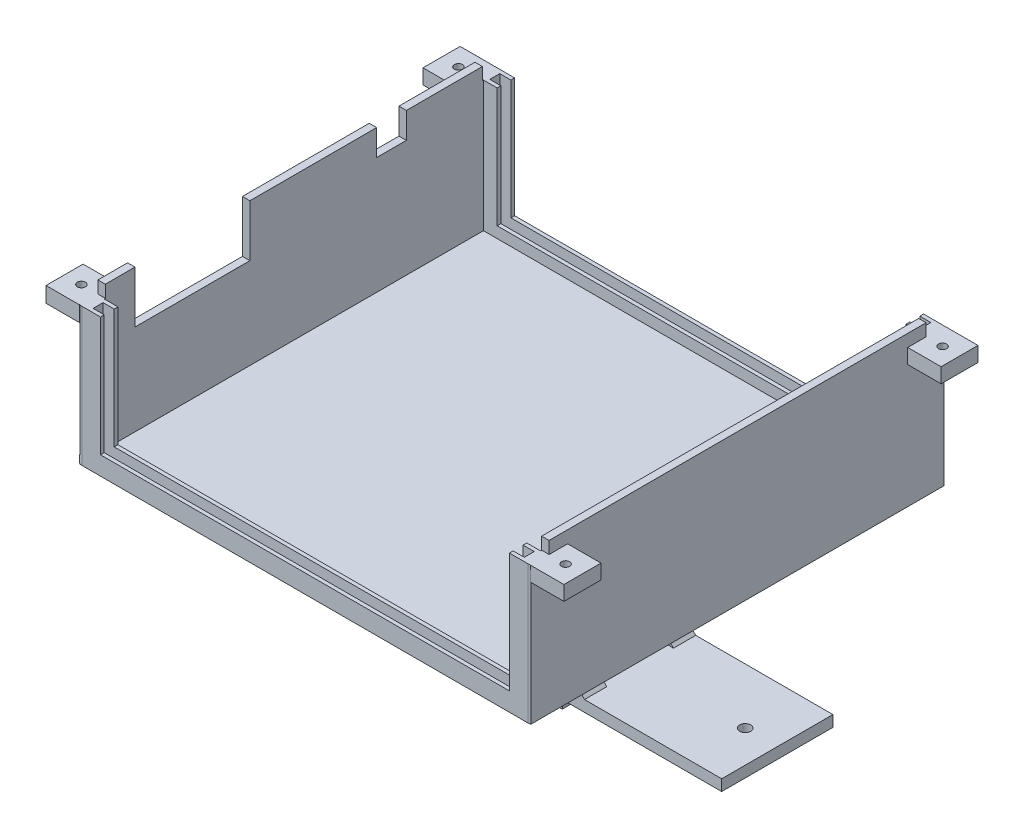
SolidWorks part; units mm, degrees
ref_plane "Front Plane" through (0, 0, 0) normal (0, 0, 1) x (1, 0, 0)
ref_plane "Top Plane" through (0, 0, 0) normal (0, 1, 0) x (1, 0, 0)
ref_plane "Right Plane" through (0, 0, 0) normal (1, 0, 0) x (0, 0, -1)
sketch "Sketch1" plane through (0, 0, 0) normal (0, 1, 0) x (1, 0, 0)
  line L1 (0, 0) -> (124.4, 0)
  line L2 (0, 0) -> (0, 111.7)
  line L3 (0, 111.7) -> (124.4, 111.7)
  line L4 (124.4, 0) -> (124.4, 111.7)
  dimension "D1" = 124.4
  dimension "D2" = 111.7
extrude "Boss-Extrude1" add sketch "Sketch1" along normal blind 2
sketch "Sketch2" plane through (0, 2, 0) normal (0, 1, 0) x (1, 0, 0)
  line L1 (124.4, 111.7) -> (0, 111.7) construction
  line L2 (123.05, 5) -> (121.05, 5)
  line L3 (123.05, 5) -> (123.05, 106.7)
  line L4 (123.05, 106.7) -> (121.05, 106.7)
  line L5 (121.05, 5) -> (121.05, 106.7)
  line L6 (124.4, 0) -> (124.4, 111.7) construction
  line L7 (0, 0) -> (124.4, 0) construction
  line L8 (0, 111.7) -> (0, 0) construction
  line L9 (3.35, 5) -> (1.35, 5)
  line L10 (3.35, 5) -> (3.35, 106.7)
  line L11 (3.35, 106.7) -> (1.35, 106.7)
  line L12 (1.35, 5) -> (1.35, 106.7)
  dimension "D1" = 2
  dimension "D2" = 5
  dimension "D3" = 1.35
  dimension "D4" = 5
  dimension "D5" = 1.35
  dimension "D6" = 2
  dimension "D7" = 5
  dimension "D8" = 5
extrude "Boss-Extrude2" add sketch "Sketch2" along normal blind 38.5
sketch "Sketch3" plane through (0, 2, 0) normal (0, 1, 0) x (1, 0, 0)
  line L1 (123.05, 0) -> (1.35, 0)
  line L2 (123.05, 0) -> (123.05, 4.7)
  line L3 (123.05, 4.7) -> (1.35, 4.7)
  line L4 (1.35, 0) -> (1.35, 4.7)
  line L5 (124.4, 0) -> (124.4, 111.7) construction
  dimension "D1" = 4.7
  dimension "D2" = 1.35
  dimension "D3" = 1.35
extrude "Boss-Extrude3" add sketch "Sketch3" along normal blind 3
sketch "Sketch5" plane through (0, 5, 0) normal (0, 1, 0) x (1, 0, 0)
  line L1 (120.35, 3.7) -> (4.05, 3.7)
  line L2 (120.35, 3.7) -> (120.35, 1)
  line L3 (120.35, 1) -> (4.05, 1)
  line L4 (4.05, 3.7) -> (4.05, 1)
  line L6 (1.35, 4.7) -> (1.35, 0) construction
  line L10 (123.05, 0) -> (123.05, 4.7) construction
  line L11 (123.05, 0) -> (123.05, 4.7) construction
  line L12 (1.35, 4.7) -> (1.35, 0) construction
  line L13 (123.05, 4.7) -> (1.35, 4.7) construction
  dimension "D2" = 2.7
  dimension "D3" = 2.7
  dimension "D4" = 2.7
  dimension "D5" = 2.7
  dimension "D6" = 2.7
  dimension "D7" = 1
  dimension "D8" = 1
extrude "Cut-Extrude8" cut sketch "Sketch5" against normal blind 3
sketch "Sketch14" plane through (0, 2, 0) normal (0, 1, 0) x (1, 0, 0)
  line L1 (1.35, 111.7) -> (123.05, 111.7)
  line L2 (1.35, 111.7) -> (1.35, 107)
  line L3 (1.35, 107) -> (123.05, 107)
  line L4 (123.05, 111.7) -> (123.05, 107)
  dimension "D1" = 4.7
  dimension "D2" = 1.35
  dimension "D3" = 1.35
extrude "Boss-Extrude6" add sketch "Sketch14" along normal blind 3
sketch "Sketch15" plane through (0, 5, 0) normal (0, 1, 0) x (1, 0, 0)
  line L1 (4.05, 110.7) -> (120.35, 110.7)
  line L2 (4.05, 110.7) -> (4.05, 108)
  line L3 (4.05, 108) -> (120.35, 108)
  line L4 (120.35, 110.7) -> (120.35, 108)
  line L8 (123.05, 107) -> (123.05, 111.7) construction
  line L9 (1.35, 106.7) -> (1.35, 5) construction
  line L10 (123.05, 111.7) -> (1.35, 111.7) construction
  dimension "D1" = 2.7
  dimension "D2" = 2.7
  dimension "D3" = 2.7
  dimension "D4" = 1
extrude "Cut-Extrude14" cut sketch "Sketch15" against normal blind 3
sketch "Sketch18" plane through (0, 2, 0) normal (0, 1, 0) x (1, 0, 0)
  line L2 (3.35, 106.7) -> (1.35, 106.7)
  line L3 (3.35, 106.7) -> (3.35, 107)
  line L4 (3.35, 107) -> (1.35, 107)
  line L5 (1.35, 106.7) -> (1.35, 107)
  line L6 (121.05, 106.7) -> (123.05, 106.7)
  line L7 (121.05, 106.7) -> (121.05, 107)
  line L8 (121.05, 107) -> (123.05, 107)
  line L9 (123.05, 106.7) -> (123.05, 107)
  line L11 (121.05, 5) -> (123.05, 5)
  line L12 (121.05, 5) -> (121.05, 4.7)
  line L13 (121.05, 4.7) -> (123.05, 4.7)
  line L14 (123.05, 5) -> (123.05, 4.7)
  line L15 (3.35, 5) -> (1.35, 5)
  line L16 (3.35, 5) -> (3.35, 4.7)
  line L17 (3.35, 4.7) -> (1.35, 4.7)
  line L18 (1.35, 5) -> (1.35, 4.7)
extrude "Boss-Extrude7" add sketch "Sketch18" along normal blind 35.2
sketch "Sketch19" plane through (0, 5, 0) normal (0, 1, 0) x (1, 0, 0)
  line L0 (1.35, 0) -> (123.05, 0) construction
  line L1 (123.05, 4.7) -> (117.35, 4.7)
  line L2 (123.05, 4.7) -> (123.05, 0)
  line L3 (123.05, 0) -> (117.35, 0)
  line L4 (117.35, 4.7) -> (117.35, 0)
  line L5 (123.05, 111.7) -> (1.35, 111.7) construction
  line L6 (1.35, 4.7) -> (7.05, 4.7)
  line L7 (1.35, 4.7) -> (1.35, 0)
  line L8 (1.35, 0) -> (7.05, 0)
  line L9 (7.05, 4.7) -> (7.05, 0)
  line L10 (123.05, 107) -> (117.35, 107)
  line L11 (123.05, 107) -> (123.05, 111.7)
  line L12 (123.05, 111.7) -> (117.35, 111.7)
  line L13 (117.35, 107) -> (117.35, 111.7)
  line L15 (1.35, 107) -> (7.05, 107)
  line L16 (1.35, 107) -> (1.35, 111.7)
  line L17 (1.35, 111.7) -> (7.05, 111.7)
  line L18 (7.05, 107) -> (7.05, 111.7)
  dimension "D1" = 5.7
  dimension "D2" = 5.7
  dimension "D3" = 5.7
  dimension "D4" = 5.7
extrude "Boss-Extrude8" add sketch "Sketch19" along normal blind 32.2
sketch "Sketch20" plane through (117.35, 0, 0) normal (-1, 0, 0) x (0, 0, 1)
  line L0 (-111.7, 37.2) -> (-107, 37.2) construction
  line L1 (-110.7, 5) -> (-108, 5)
  line L2 (-110.7, 5) -> (-110.7, 37.2)
  line L3 (-110.7, 37.2) -> (-108, 37.2)
  line L4 (-108, 5) -> (-108, 37.2)
  dimension "D1" = 2.7
extrude "Cut-Extrude15" cut sketch "Sketch20" against normal blind 3
sketch "Sketch21" plane through (7.05, 0, 0) normal (1, 0, 0) x (0, 0, -1)
  line L0 (107, 37.2) -> (111.7, 37.2) construction
  line L1 (108, 5) -> (110.7, 5)
  line L2 (108, 5) -> (108, 37.2)
  line L3 (108, 37.2) -> (110.7, 37.2)
  line L4 (110.7, 5) -> (110.7, 37.2)
  dimension "D1" = 2.7
extrude "Cut-Extrude16" cut sketch "Sketch21" against normal blind 3
sketch "Sketch24" plane through (7.05, 0, 0) normal (1, 0, 0) x (0, 0, -1)
  line L0 (0, 37.2) -> (4.7, 37.2) construction
  line L1 (1, 5) -> (3.7, 5)
  line L2 (1, 5) -> (1, 37.2)
  line L3 (1, 37.2) -> (3.7, 37.2)
  line L4 (3.7, 5) -> (3.7, 37.2)
  dimension "D1" = 2.7
extrude "Cut-Extrude18" cut sketch "Sketch24" against normal blind 3
sketch "Sketch25" plane through (117.35, 0, 0) normal (-1, 0, 0) x (0, 0, 1)
  line L0 (-4.7, 37.2) -> (0, 37.2) construction
  line L1 (-3.7, 5) -> (-1, 5)
  line L2 (-3.7, 5) -> (-3.7, 37.2)
  line L3 (-3.7, 37.2) -> (-1, 37.2)
  line L4 (-1, 5) -> (-1, 37.2)
  dimension "D1" = 2.7
extrude "Cut-Extrude19" cut sketch "Sketch25" against normal blind 3
sketch "Sketch30" plane through (1.35, 0, 0) normal (-1, 0, 0) x (0, 0, 1)
  line L0 (-106.7, 37.2) -> (-106.7, 3.1848) construction
  line L1 (-5, 37.2) -> (-5, 3.1848) construction
  line L2 (-106.7, 37.2) -> (-5, 37.2) construction
  line L3 (-86.2, 40.5) -> (-86.2, 2) construction
  line L4 (-13, 40.5) -> (-44, 40.5)
  line L5 (-13, 40.5) -> (-13, 26.5)
  line L6 (-13, 26.5) -> (-44, 26.5)
  line L7 (-44, 40.5) -> (-44, 26.5)
  line L8 (-106.7, 40.5) -> (-5, 40.5) construction
  line L9 (-111.7, 2) -> (0, 2) construction
  line L10 (-78.2, 40.5) -> (-78.2, 2) construction
  line L12 (-86.2, 40.5) -> (-78.2, 40.5)
  line L13 (-86.2, 40.5) -> (-86.2, 33.5)
  line L14 (-86.2, 33.5) -> (-78.2, 33.5)
  line L15 (-78.2, 40.5) -> (-78.2, 33.5)
  dimension "D1" = 31
  dimension "D2" = 13
  dimension "D3" = 0
  dimension "D4" = 14
  dimension "D5" = 25.5
  dimension "D6" = 8
  dimension "D7" = 7
extrude "Cut-Extrude23" cut sketch "Sketch30" against normal blind 2
sketch "Sketch31" plane through (123.05, 0, 0) normal (1, 0, 0) x (0, 0, -1)
  line L0 (0, 2) -> (111.7, 2) construction
  line L1 (6, 38.2) -> (0, 38.2)
  line L2 (6, 38.2) -> (6, 2)
  line L3 (6, 2) -> (0, 2)
  line L4 (0, 38.2) -> (0, 2)
  line L5 (105.7, 38.2) -> (111.7, 38.2)
  line L6 (105.7, 38.2) -> (105.7, 2)
  line L7 (105.7, 2) -> (111.7, 2)
  line L8 (111.7, 38.2) -> (111.7, 2)
  line L9 (111.7, 2) -> (111.7, 0) construction
  dimension "D1" = 6
  dimension "D2" = 6
extrude "Boss-Extrude9" add sketch "Sketch31" along normal blind 1.35
fillet "Fillet1" radius 2 4 edges at (0, 1, 0) (124.4, 19.1, 0) (124.4, 19.1, -111.7) (0, 1, -111.7)
sketch "Sketch33" plane through (123.05, 0, 0) normal (1, 0, 0) x (0, 0, -1)
  line L0 (105.7, 38.2) -> (105.7, 2) construction
  line L1 (6, 2) -> (105.7, 2)
  line L2 (6, 2) -> (6, 5)
  line L3 (6, 5) -> (105.7, 5)
  line L4 (105.7, 2) -> (105.7, 5)
  dimension "D1" = 3
extrude "Boss-Extrude11" add sketch "Sketch33" along normal blind 1.35
sketch "Sketch43" plane through (0, 37.2, 0) normal (0, 1, 0) x (1, 0, 0)
  line L1 (0, 112.2322) -> (1.2298, 112.2322)
  line L2 (0, 112.2322) -> (0, 0.1542)
  line L3 (0, 0.1542) -> (1.2298, 0.1542)
  line L4 (1.2298, 112.2322) -> (1.2298, 0.1542)
  arc A0 (1.35, 0.1086) -> (2, 0) centre (2, 2) ccw construction
extrude "Cut-Extrude25" cut sketch "Sketch43" against normal through all
sketch "Sketch47" plane through (0, 0, 0) normal (0, -1, 0) x (-1, 0, 0)
  line L1 (-33.64, 40.85) -> (-90.76, 40.85)
  line L2 (-33.64, 40.85) -> (-33.64, 70.85)
  line L3 (-33.64, 70.85) -> (-90.76, 70.85)
  line L4 (-90.76, 40.85) -> (-90.76, 70.85)
  line L5 (-33.64, 40.85) -> (-90.76, 70.85) construction
  line L6 (-33.64, 70.85) -> (-90.76, 40.85) construction
  point P0 (-62.2, 55.85)
extrude "Boss-Extrude22" add sketch "Sketch47" along normal blind 38
sketch "Sketch49" plane through (0, -38, 0) normal (0, -1, 0) x (-1, 0, 0)
  line L0 (-90.76, 40.85) -> (-33.64, 40.85) construction
  line L1 (-36.64, 40.85) -> (-87.76, 40.85)
  line L2 (-36.64, 40.85) -> (-36.64, 70.85)
  line L3 (-36.64, 70.85) -> (-87.76, 70.85)
  line L4 (-87.76, 40.85) -> (-87.76, 70.85)
  line L5 (-33.64, 70.85) -> (-90.76, 70.85) construction
extrude "Cut-Extrude30" cut sketch "Sketch49" against normal blind 38
sketch "Sketch51" plane through (0, 38.2, 0) normal (0, 1, 0) x (1, 0, 0)
  line L1 (123.05, 0.1086) -> (125.4021, 0.1086)
  line L2 (123.05, 0.1086) -> (123.05, 112.4909)
  line L3 (123.05, 112.4909) -> (125.4021, 112.4909)
  line L4 (125.4021, 0.1086) -> (125.4021, 112.4909)
extrude "Cut-Extrude33" cut sketch "Sketch51" against normal through all
sketch "Sketch54" plane through (1.35, 0, 0) normal (-1, 0, 0) x (0, 0, 1)
  line L1 (-5, 37.2) -> (-0.1086, 37.2) construction
  line L3 (0, 37.2) -> (0, 0) construction
  line L4 (-10, 37.2) -> (0, 37.2)
  line L5 (-10, 37.2) -> (-10, 33.0343)
  line L6 (0, 37.2) -> (0, 33.0343)
  line L7 (-10, 33.0343) -> (0, 33.0343)
  line L8 (-111.7, 0) -> (-111.7, 37.2) construction
  line L9 (-111.5914, 37.2) -> (-106.7, 37.2) construction
  line L10 (-101.7, 37.2) -> (-111.7, 37.2)
  line L11 (-101.7, 37.2) -> (-101.7, 33.1834)
  line L12 (-111.7, 37.2) -> (-111.7, 33.1834)
  line L13 (-101.7, 33.1834) -> (-111.7, 33.1834)
  point P0 (0, 33.2)
  point P1 (-111.7, 37.2)
  point P3 (-10, 37.2)
  point P6 (0, 37.2)
  point P12 (-111.7, 33.2)
  point P16 (-101.7, 37.2)
  dimension "D1" = 10
  dimension "D2" = 4
  dimension "D3" = 10
  dimension "D4" = 4
extrude "Boss-Extrude23" add sketch "Sketch54" along normal blind 9
sketch "Sketch55" plane through (123.05, 0, 0) normal (1, 0, 0) x (0, 0, -1)
  line L0 (0.1086, 37.2) -> (5, 37.2) construction
  line L1 (0, 0) -> (0, 37.2) construction
  line L2 (10, 37.2) -> (0, 37.2)
  line L3 (10, 37.2) -> (10, 33.2492)
  line L4 (0, 37.2) -> (0, 33.2492)
  line L5 (10, 33.2492) -> (0, 33.2492)
  line L6 (111.7, 37.2) -> (111.7, 0) construction
  line L7 (106.7, 37.2) -> (111.5914, 37.2) construction
  line L8 (111.7, 33.2) -> (111.7, 37.2)
  line L9 (111.7, 33.2) -> (101.7487, 33.2)
  line L10 (111.7, 37.2) -> (101.7487, 37.2)
  line L11 (101.7487, 33.2) -> (101.7487, 37.2)
  point P0 (0, 37.2)
  point P1 (10, 37.2)
  point P3 (0, 33.2)
  point P6 (111.7, 37.2)
  point P11 (111.7, 33.2)
  point P15 (101.7, 37.2)
  dimension "D1" = 10
  dimension "D2" = 4
  dimension "D3" = 10
  dimension "D4" = 4
extrude "Boss-Extrude24" add sketch "Sketch55" along normal blind 9
sketch "Sketch56" plane through (0, 37.2, 0) normal (0, 1, 0) x (1, 0, 0)
  line L0 (-7.65, -990) -> (-7.65, 49010) construction
  line L1 (132.05, -990) -> (132.05, 49010) construction
  line L2 (-1007.65, 0) -> (48992.35, 0) construction
  line L3 (-1007.65, 111.7) -> (48992.35, 111.7) construction
  circle A0 centre (-3.1, 106.7) radius 1.1
  circle A1 centre (127.5, 106.7) radius 1.1
  circle A2 centre (127.5, 5) radius 1.1
  circle A3 centre (-3.1, 5) radius 1.1
  point P10 (-7.65, 106.7)
  point P13 (132.05, 106.7)
  point P14 (132.05, 5)
  point P15 (-7.65, 5)
  point P16 (-3.1, 111.7)
  point P17 (127.5, 0)
  point P20 (127.5, 111.7)
  point P21 (-3.1, 0)
  point P22 (-3.1, 106.7)
  point P23 (127.5, 106.7)
  point P24 (127.5, 5)
  point P25 (-3.1, 5)
  dimension "D1" = 5
  dimension "D2" = 5
  dimension "D3" = 5
  dimension "D4" = 5
  dimension "D5" = 4.55
  dimension "D6" = 4.55
  dimension "D7" = 4.55
  dimension "D8" = 4.55
extrude "Cut-Extrude34" cut sketch "Sketch56" against normal blind 10
sketch "Sketch57" plane through (90.76, 0, 0) normal (1, 0, 0) x (0, 0, -1)
  line L0 (40.85, -38) -> (40.85, 0) construction
  line L1 (70.85, -38) -> (70.85, 0) construction
  circle A0 centre (45.85, -34) radius 1
  circle A1 centre (65.85, -34) radius 1
  point P0 (40.85, -38)
  point P1 (40.85, -34)
  point P3 (45.85, -34)
  point P6 (70.85, -34)
  point P8 (65.85, -34)
  dimension "D1" = 4
  dimension "D2" = 5
  dimension "D3" = 5
extrude "Cut-Extrude35" cut sketch "Sketch57" against normal through all
sketch "Sketch58" plane through (90.76, 0, 0) normal (1, 0, 0) x (0, 0, -1)
  line L0 (70.85, -38) -> (70.85, 0) construction
  line L1 (40.85, -38) -> (40.85, 0) construction
  line L2 (70.85, -30.75) -> (40.85, -30.75)
  line L3 (70.85, -30.75) -> (70.85, -27.75)
  line L4 (70.85, -27.75) -> (40.85, -27.75)
  line L5 (40.85, -27.75) -> (40.85, -30.75)
  line L6 (40.85, -30.75) -> (40.85, -27.75)
  circle A0 centre (65.85, -34) radius 1 construction
  circle A1 centre (45.85, -34) radius 1 construction
  point P0 (65.85, -33)
  point P1 (45.85, -33)
  point P4 (45.85, -30.75)
  point P7 (65.85, -30.75)
  point P8 (70.85, -30.75)
  point P9 (40.85, -30.75)
  point P16 (70.85, -27.75)
  point P17 (40.85, -27.75)
  line M4 (40.85, 0) -> (40.85, -38)
  line M6 (70.85, -38) -> (70.85, 0)
  dimension "D1" = 2.25
  dimension "D2" = 2.25
  dimension "D3" = 3
  dimension "D4" = 3
extrude "Boss-Extrude25" add sketch "Sketch58" along normal blind 43 contours L4 L2 M6 M4
sketch "Sketch59" plane through (33.64, 0, 0) normal (-1, 0, 0) x (0, 0, 1)
  line L0 (-40.85, -38) -> (-40.85, 0) construction
  line L1 (-70.85, -38) -> (-70.85, 0) construction
  line L2 (-40.85, -30.75) -> (-70.85, -30.75)
  line L3 (-40.85, -30.75) -> (-40.85, -27.7284)
  line L4 (-70.85, -30.75) -> (-70.85, -27.7284)
  line L5 (-40.85, -27.7284) -> (-70.85, -27.7284)
  point P0 (-40.85, -30.75)
  point P1 (-70.85, -30.75)
  point P4 (-70.85, -27.75)
  dimension "D1" = 7.25
  dimension "D2" = 10.25
  dimension "D3" = 7.25
extrude "Boss-Extrude26" add sketch "Sketch59" along normal blind 43
sketch "Sketch60" plane through (0, 0, -40.85) normal (0, 0, 1) x (1, 0, 0)
  line L0 (-9.36, -27.7284) -> (33.64, -27.7284) construction
  line L1 (33.64, -27.7284) -> (33.64, 0) construction
  line L2 (27.64, -27.7284) -> (33.64, -21.7284)
  line L3 (33.64, -21.7284) -> (33.64, -27.7284)
  line L4 (33.64, -27.7284) -> (27.64, -27.7284)
  point P0 (27.64, -27.7284)
  point P1 (33.64, -21.7284)
  dimension "D1" = 6
  dimension "D2" = 6
sketch "Sketch61" plane through (0, 0, -40.85) normal (0, 0, 1) x (1, 0, 0)
  line L0 (133.76, -27.75) -> (90.76, -27.75) construction
  line L1 (90.76, -27.75) -> (90.76, 0) construction
  line L2 (90.76, -21.75) -> (96.76, -27.75)
  line L3 (96.76, -27.75) -> (90.76, -27.75)
  line L4 (90.76, -27.75) -> (90.76, -21.75)
  point P0 (96.76, -27.75)
  point P1 (90.76, -21.75)
  dimension "D1" = 6
  dimension "D2" = 6
extrude "Boss-Extrude28" add sketch "Sketch61" against normal blind 6
sketch "Sketch62" plane through (0, 0, -70.85) normal (0, 0, -1) x (-1, 0, 0)
  line L0 (-133.76, -27.75) -> (-90.76, -27.75) construction
  line L1 (-90.76, -27.75) -> (-90.76, 0) construction
  line L2 (-90.76, -21.75) -> (-90.76, -27.75)
  line L3 (-90.76, -27.75) -> (-96.76, -27.75)
  line L4 (-96.76, -27.75) -> (-90.76, -21.75)
  point P0 (-96.76, -27.75)
  point P1 (-90.76, -21.75)
  dimension "D1" = 6
  dimension "D2" = 6
extrude "Boss-Extrude29" add sketch "Sketch62" against normal blind 6
extrude "Boss-Extrude30" add sketch "Sketch60" against normal blind 6
sketch "Sketch63" plane through (0, 0, -70.85) normal (0, 0, -1) x (-1, 0, 0)
  line L0 (9.36, -27.7284) -> (-33.64, -27.7284) construction
  line L1 (-33.64, -27.7284) -> (-33.64, 0) construction
  line L2 (-33.64, -22.0694) -> (-33.64, -27.7284)
  line L3 (-33.64, -27.7284) -> (-27.64, -27.7284)
  line L4 (-27.64, -27.7284) -> (-33.64, -22.0694)
  point P0 (-27.64, -27.7284)
  point P1 (-33.64, -22.0694)
  dimension "D1" = 5.659
  dimension "D2" = 6
extrude "Boss-Extrude31" add sketch "Sketch63" against normal blind 6
sketch "Sketch64" plane through (33.64, 0, 0) normal (-1, 0, 0) x (0, 0, 1)
  line L0 (-40.85, -38) -> (-40.85, -30.75) construction
  line L1 (-70.85, -38) -> (-70.85, -30.75) construction
  line L2 (-70.85, -33) -> (-40.85, -33)
  line L3 (-70.85, -33) -> (-70.85, -39.5461)
  line L4 (-40.85, -33) -> (-40.85, -39.5461)
  line L5 (-70.85, -39.5461) -> (-40.85, -39.5461)
  circle A0 centre (-65.85, -34) radius 1 construction
  circle A1 centre (-45.85, -34) radius 1 construction
  point P0 (-65.85, -33)
  point P1 (-45.85, -33)
  point P4 (-40.85, -33)
  point P7 (-70.85, -33)
extrude "Cut-Extrude36" cut sketch "Sketch64" against normal through all
sketch "Sketch65" plane through (0, -30.75, 0) normal (0, -1, 0) x (-1, 0, 0)
  line L0 (-90.76, 70.85) -> (-90.76, 40.85) construction
  circle A0 centre (-125.11, 55.85) radius 1.5
  point P0 (-90.76, 55.85)
  point P1 (-125.11, 55.85)
  dimension "D1" = 15
  dimension "D2" = 34.35
extrude "Cut-Extrude37" cut sketch "Sketch65" against normal blind 6
sketch "Sketch67" plane through (0, -30.75, 0) normal (0, -1, 0) x (1, 0, 0)
  line L0 (-9.36, -70.85) -> (-9.36, -40.85) construction
  circle A0 centre (-0.71, -55.85) radius 1.5
  point P0 (-9.36, -55.85)
  point P1 (-2.21, -55.85)
  point P4 (-0.71, -55.85)
  dimension "D1" = 7.15
  dimension "D2" = 1.5
extrude "Cut-Extrude39" cut sketch "Sketch67" against normal blind 6
